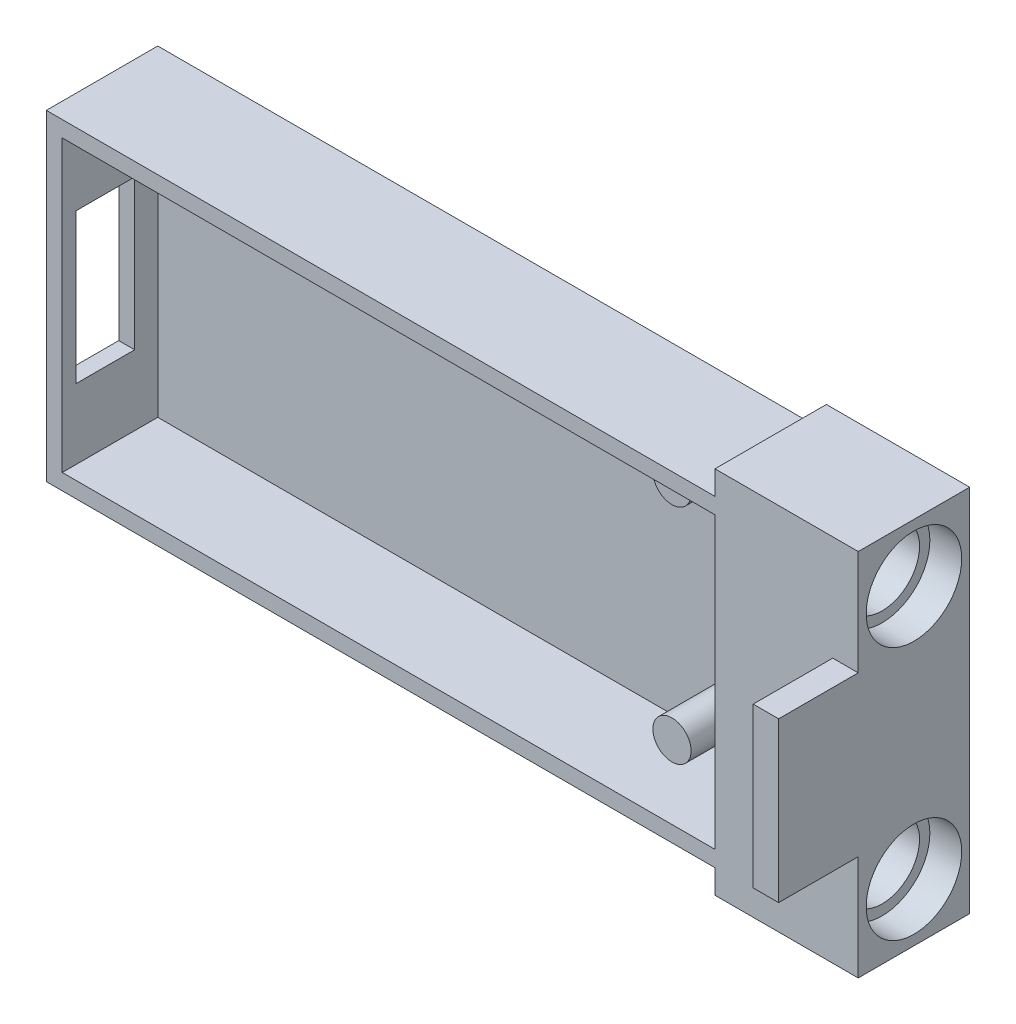
SolidWorks part; units mm, degrees
ref_plane "Front Plane" through (0, 0, 0) normal (0, 0, 1) x (1, 0, 0)
ref_plane "Top Plane" through (0, 0, 0) normal (0, 1, 0) x (1, 0, 0)
ref_plane "Right Plane" through (0, 0, 0) normal (1, 0, 0) x (0, 0, -1)
sketch "Sketch1" plane through (0, 0, 0) normal (0, 0, 1) x (1, 0, 0)
  line L1 (-19.5, -10.1) -> (19.5, -10.1)
  line L2 (-19.5, -10.1) -> (-19.5, 10.1)
  line L3 (-19.5, 10.1) -> (19.5, 10.1)
  line L4 (19.5, -10.1) -> (19.5, 10.1)
  line L5 (-19.5, -10.1) -> (19.5, 10.1) construction
  line L6 (-19.5, 10.1) -> (19.5, -10.1) construction
  point P0 (0, 0)
  dimension "D1" = 20.2
  dimension "D2" = 39
extrude "Boss-Extrude1" add sketch "Sketch1" along normal blind 7
sketch "Sketch2" plane through (0, 0, 7) normal (0, 0, 1) x (1, 0, 0)
  line L0 (19.5, -10.1) -> (19.5, 10.1) construction
  line L1 (19.5, 9.1) -> (-18.5, 9.1)
  line L2 (19.5, 9.1) -> (19.5, -9.1)
  line L3 (19.5, -9.1) -> (-18.5, -9.1)
  line L4 (-18.5, 9.1) -> (-18.5, -9.1)
  line L5 (-19.5, 10.1) -> (-19.5, -10.1) construction
  line L6 (19.5, 10.1) -> (-19.5, 10.1) construction
  line L7 (-19.5, -10.1) -> (19.5, -10.1) construction
  dimension "D1" = 1
  dimension "D2" = 1
  dimension "D3" = 1
extrude "Cut-Extrude1" cut sketch "Sketch2" against normal blind 6
sketch "Sketch3" plane through (0, 0, 1) normal (0, 0, 1) x (1, 0, 0)
  line L0 (19.5, -9.1) -> (19.5, 9.1) construction
  line L1 (-18.5, -9.1) -> (19.5, -9.1) construction
  circle A0 centre (17.3, -7) radius 1.2
  circle A1 centre (17.3, 7) radius 1.2
  dimension "D1" = 2.4
  dimension "D2" = 2.2
  dimension "D3" = 2.1
  dimension "D4" = 14
extrude "spunt" add sketch "Sketch3" along normal blind 3.5
sketch "Sketch5" plane through (-18.5, 0, 0) normal (1, 0, 0) x (0, 0, -1)
  line L0 (-1, -9.1) -> (-1, 9.1) construction
  line L1 (-6.15, -4.7) -> (-2.45, -4.7)
  line L2 (-6.15, -4.7) -> (-6.15, 4.7)
  line L3 (-6.15, 4.7) -> (-2.45, 4.7)
  line L4 (-2.45, -4.7) -> (-2.45, 4.7)
  line L6 (-7, 9.1) -> (-7, -9.1) construction
  point P10 (-7, 0)
  point P11 (-6.15, 0)
  dimension "D1" = 9.4
  dimension "D2" = 3.7
  dimension "D3" = 1.45
extrude "usbc" cut sketch "Sketch5" against normal blind 22
sketch "Sketch6" plane through (19.5, 0, 0) normal (1, 0, 0) x (0, 0, -1)
  line L5 (0, -10.1) -> (0, 10.1) construction
  line L6 (0, -10.1) -> (-7, -10.1)
  line L7 (0, -10.1) -> (0, -9.1)
  line L8 (0, -9.1) -> (-7, -9.1)
  line L9 (-7, -10.1) -> (-7, -9.1)
  line L10 (0, 9.1) -> (-7, 9.1)
  line L11 (0, 9.1) -> (0, 10.1)
  line L12 (0, 10.1) -> (-7, 10.1)
  line L13 (-7, 9.1) -> (-7, 10.1)
  line L15 (-1, 9.1) -> (0, 9.1)
  line L16 (-1, 9.1) -> (-1, -9.1)
  line L17 (-1, -9.1) -> (0, -9.1)
  line L18 (0, 9.1) -> (0, -9.1)
  line M9 (-1, 9.1) -> (-1, -9.1)
  line M10 (-1, -9.1) -> (-7, -9.1)
  line M11 (-7, -9.1) -> (-7, -10.1)
  line M12 (-7, -10.1) -> (0, -10.1)
  line M13 (0, -10.1) -> (0, 10.1)
  dimension "D1" = 1
  dimension "D2" = 1
extrude "rozsireni drzaku" add sketch "Sketch6" along normal blind 3 contours L10 L8 M13 M9 | L8 M13 M10 M11 M12
sketch "Sketch7" plane through (22.5, 0, 0) normal (1, 0, 0) x (0, 0, -1)
  line L0 (0, -10.1) -> (0, 10.1) construction
  line L5 (-7, 11.6) -> (0, 11.6)
  line L6 (-7, 11.6) -> (-7, -11.6)
  line L7 (-7, -11.6) -> (0, -11.6)
  line L8 (0, 11.6) -> (0, -11.6)
  line L9 (-7, 9.1) -> (-7, -9.1) construction
  line L10 (0, 10.1) -> (-7, 10.1) construction
  line L11 (-7, -10.1) -> (0, -10.1) construction
  dimension "D1" = 0
  dimension "D2" = 0
  dimension "D3" = 1.5
  dimension "D4" = 1.5
extrude "drzak" add sketch "Sketch7" along normal blind 9
sketch "Sketch8" plane through (31.5, 0, 0) normal (1, 0, 0) x (0, 0, -1)
  line L0 (-7, 11.6) -> (0, 11.6) construction
  line L2 (-7, 11.6) -> (-7, -11.6) construction
  circle A0 centre (-3.5, 7.97) radius 2.35
  circle A1 centre (-3.5, -7.97) radius 2.35
  point P7 (-3.5, 11.6)
  point P9 (-7, 0)
  dimension "D1" = 4.7
  dimension "D2" = 15.94
  dimension "D3" = 7.97
extrude "zakladni dira" cut sketch "Sketch8" against normal blind 9
sketch "Sketch9" plane through (31.5, 0, 0) normal (1, 0, 0) x (0, 0, -1)
  circle A0 centre (-3.5, 7.97) radius 3
  circle A1 centre (-3.5, -7.97) radius 3
  dimension "D1" = 6
extrude "Cut-Extrude4" cut sketch "Sketch9" against normal blind 2
sketch "Sketch11" plane through (22.5, 0, 0) normal (-1, 0, 0) x (0, 0, 1)
  circle A0 centre (3.5, -7.97) radius 3
  circle A1 centre (3.5, 7.97) radius 3
  dimension "D1" = 6
extrude "Cut-Extrude5" cut sketch "Sketch11" against normal blind 1
sketch "Sketch10" plane through (0, 0, 7) normal (0, 0, 1) x (1, 0, 0)
  line L5 (31.5, 11.6) -> (31.5, -11.6) construction
  line L6 (31.5, 5) -> (29.9, 5)
  line L7 (31.5, 5) -> (31.5, -5)
  line L8 (31.5, -5) -> (29.9, -5)
  line L9 (29.9, 5) -> (29.9, -5)
  line L10 (22.5, 9.1) -> (22.5, -9.1) construction
  point P9 (22.5, 0)
  point P10 (29.9, 0)
  dimension "D1" = 10
  dimension "D2" = 1.6
extrude "podstava" add sketch "Sketch10" along normal blind 5
